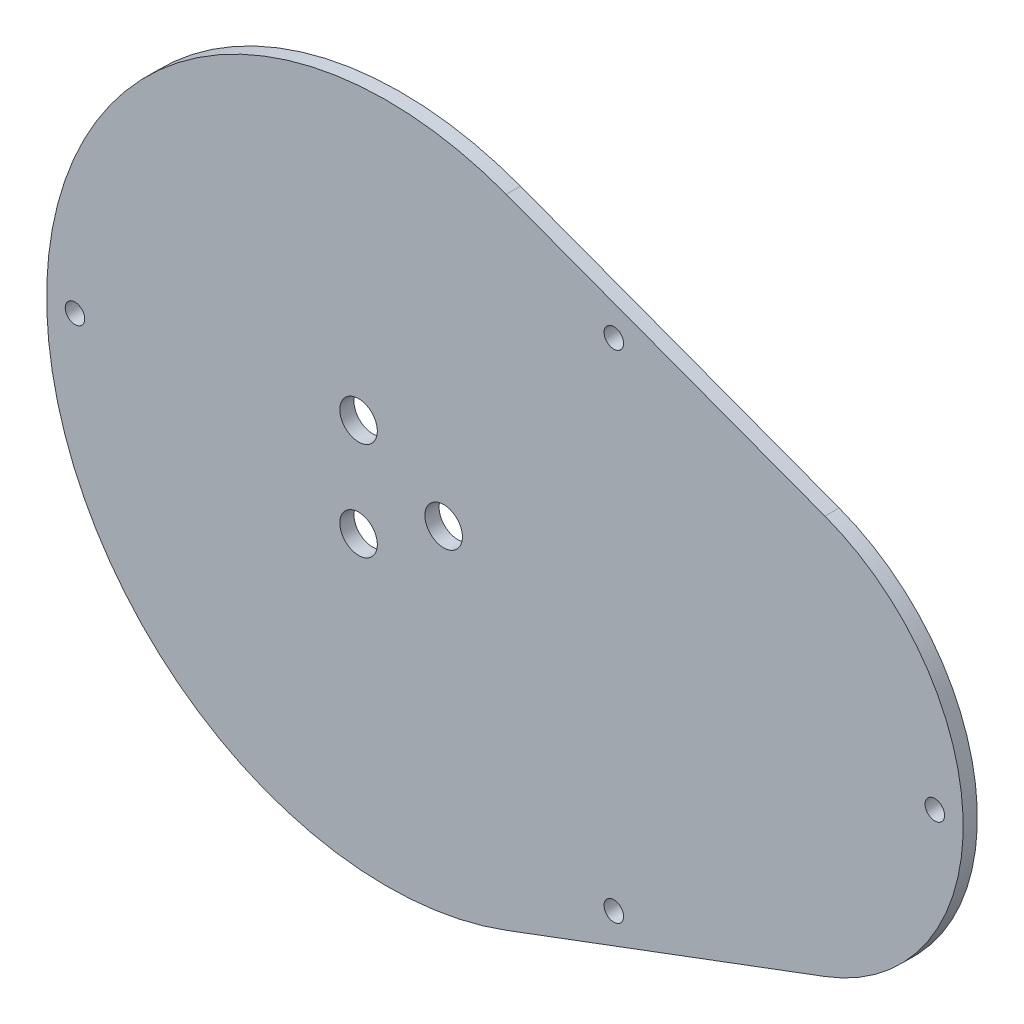
SolidWorks part; units mm, degrees
ref_plane "Front Plane" through (0, 0, 0) normal (0, 0, 1) x (1, 0, 0)
ref_plane "Top Plane" through (0, 0, 0) normal (0, 1, 0) x (1, 0, 0)
ref_plane "Right Plane" through (0, 0, 0) normal (1, 0, 0) x (0, 0, -1)
sketch "Sketch1" plane through (0, 0, 0) normal (0, 0, 1) x (1, 0, 0)
  line L0 (0, 0) -> (238.76, 0) construction
  line L1 (0, 0) -> (15.1623, -83.7282) construction
  line L2 (15.1623, -83.7282) -> (238.76, 0) construction
  line L3 (0, 0) -> (15.1623, 83.7282) construction
  line L4 (15.1623, 83.7282) -> (238.76, 0) construction
  line L5 (14.4743, 38.6539) -> (50.1548, 25.293) construction
  line L6 (14.4743, -38.6539) -> (50.1548, -25.293) construction
  line L7 (13.3609, 35.6805) -> (49.0414, 22.3196)
  line L8 (13.3609, -35.6805) -> (49.0414, -22.3196)
  arc A0 (14.4743, 38.6539) -> (14.4743, -38.6539) centre (0, 0) ccw construction
  arc A1 (50.1548, -25.293) -> (50.1548, 25.293) centre (40.6836, 0) ccw construction
  arc A2 (49.0414, -22.3196) -> (49.0414, 22.3196) centre (40.6836, 0) ccw
  arc A3 (13.3609, 35.6805) -> (13.3609, -35.6805) centre (0, 0) ccw
  circle A4 centre (61.3417, 0) radius 1.0922
  circle A5 centre (25.4, 27.782) radius 1.0922
  circle A6 centre (25.4, -27.782) radius 1.0922
  circle A7 centre (-34.925, 0) radius 1.0922
  circle A8 centre (0, 0) radius 6.35 construction
  circle A9 centre (6.35, 0) radius 2.1
  circle A10 centre (-3.175, -5.4993) radius 2.1
  circle A11 centre (-3.175, 5.4993) radius 2.1
  point P33 (0, 0)
  dimension "D2" = 82.55
  dimension "D7" = 2.1844
  dimension "D14" = 12.7
  dimension "D15" = 4.2
  dimension "D3" = 85.09
  dimension "D4" = 238.76
  dimension "D5" = 38.1
  dimension "D6" = 3.175
  dimension "D8" = 3.175
  dimension "D9" = 3.175
  dimension "D10" = 3.175
  dimension "D11" = 3.175
  dimension "D12" = 25.4
  dimension "D13" = 25.4
  dimension "D16" = 3
extrude "Boss-Extrude1" add sketch "Sketch1" along normal blind 1.5875
